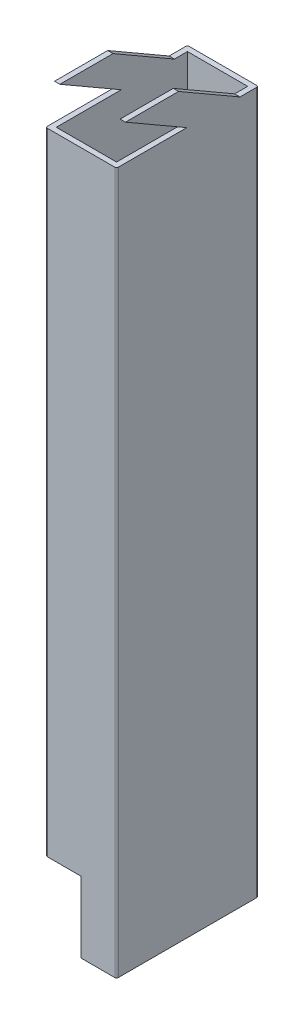
SolidWorks part; units mm, degrees
ref_plane "Front Plane" through (0, 0, 0) normal (0, 0, 1) x (1, 0, 0)
ref_plane "Top Plane" through (0, 0, 0) normal (0, 1, 0) x (1, 0, 0)
ref_plane "Right Plane" through (0, 0, 0) normal (1, 0, 0) x (0, 0, -1)
sketch "Sketch1" plane through (0, 0, 0) normal (0, 1, 0) x (1, 0, 0)
  line L0 (1.5, 1.5) -> (18.5, 1.5)
  line L1 (0.5, 0) -> (19.5, 0)
  line L2 (0, 0.5) -> (0, 39.5)
  line L3 (0.5, 40) -> (19.5, 40)
  line L4 (20, 0.5) -> (20, 39.5)
  line L5 (18.5, 1.5) -> (18.5, 38.5)
  line L6 (1.5, 38.5) -> (18.5, 38.5)
  line L7 (1.5, 1.5) -> (1.5, 38.5)
  arc A0 (19.5, 0) -> (20, 0.5) centre (19.5, 0.5) ccw
  arc A1 (0.5, 0) -> (0, 0.5) centre (0.5, 0.5) cw
  arc A2 (0, 39.5) -> (0.5, 40) centre (0.5, 39.5) cw
  arc A3 (19.5, 40) -> (20, 39.5) centre (19.5, 39.5) cw
  arc A4 (18.5, 1.5) -> (18.5, 1.5) centre (18.5, 1.5) ccw
  arc A5 (18.5, 38.5) -> (18.5, 38.5) centre (18.5, 38.5) cw
  arc A6 (1.5, 38.5) -> (1.5, 38.5) centre (1.5, 38.5) cw
  arc A7 (1.5, 1.5) -> (1.5, 1.5) centre (1.5, 1.5) cw
  point P9 (0, 0)
  dimension "D3" = 0.5
  dimension "D1" = 20
  dimension "D2" = 40
  dimension "D4" = 1.5
extrude "Boss-Extrude1" add sketch "Sketch1" along normal blind 208
sketch "Sketch2" plane through (0, 0, 0) normal (0, 0, 1) x (1, 0, 0)
  line L10 (0, 0) -> (10, 0)
  line L11 (0.5, 0) -> (19.5, 0) construction
  line L12 (10, 0) -> (10, 20)
  line L13 (10, 20) -> (0, 20)
  line L14 (0, 208) -> (0, 0) construction
  line L15 (0, 20) -> (0, 0)
  dimension "D1" = 20
extrude "Cut-Extrude1" cut sketch "Sketch2" against normal blind 40
sketch "Sketch3" plane through (0, 0, 0) normal (1, 0, 0) x (0, 0, -1)
  line L6 (0, 208) -> (0, 198)
  line L7 (0, 208) -> (0, 20) construction
  line L8 (0, 198) -> (19.8205, 198)
  line L9 (19.8205, 198) -> (2.5, 208)
  line L10 (39.5, 208) -> (0.5, 208) construction
  line L11 (2.5, 208) -> (0, 208)
  line L12 (17.5, 208) -> (34.8205, 198)
  line L13 (34.8205, 198) -> (40, 198)
  line L14 (40, 208) -> (40, 20) construction
  line L15 (40, 198) -> (40, 208)
  line L16 (40, 208) -> (17.5, 208)
  dimension "D1" = 15
  dimension "D2" = 10
  dimension "D3" = 30
  dimension "10" = 2.5
extrude "Cut-Extrude2" cut sketch "Sketch3" along normal blind 40
